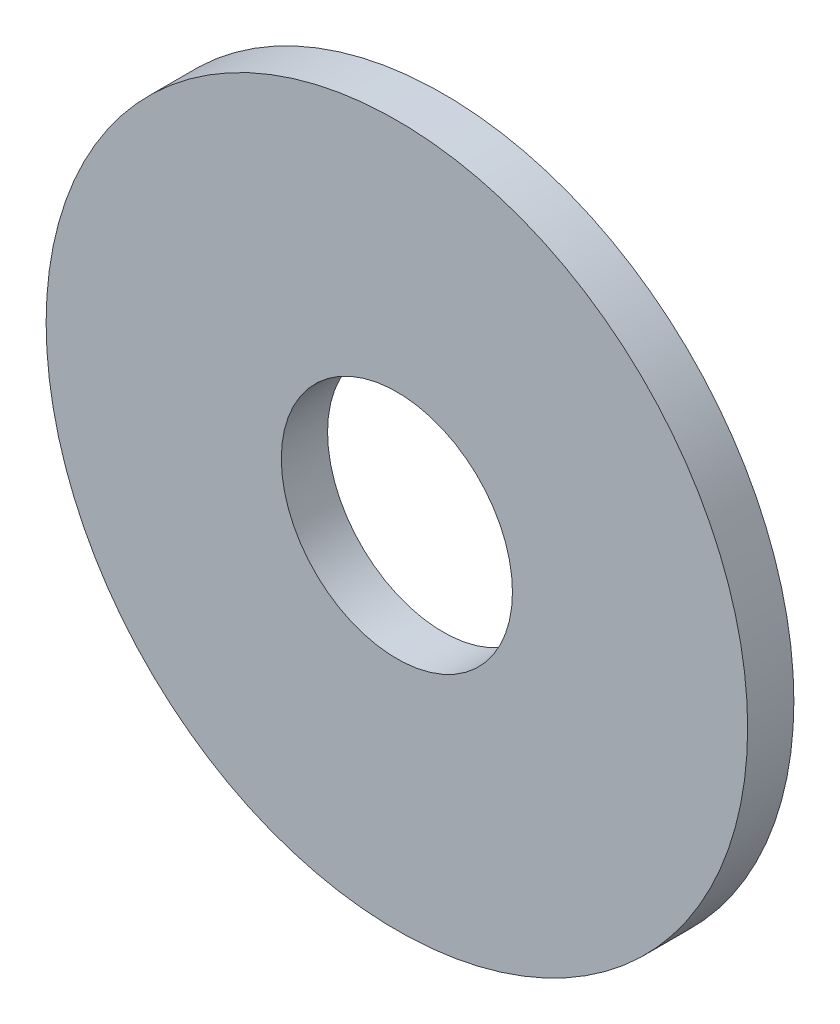
SolidWorks part; units mm, degrees
material "1060 Alloy"
ref_plane "Front Plane" through (0, 0, 0) normal (0, 0, 1) x (1, 0, 0)
ref_plane "Top Plane" through (0, 0, 0) normal (0, 1, 0) x (1, 0, 0)
ref_plane "Right Plane" through (0, 0, 0) normal (1, 0, 0) x (0, 0, -1)
sketch "Sketch1" plane through (0, 0, 0) normal (0, 0, 1) x (1, 0, 0)
  circle A0 centre (0, 0) radius 7.5875
  circle A1 centre (0, 0) radius 2.5
  dimension "D1" = 15.175
  dimension "D2" = 5
extrude "Boss-Extrude1" add sketch "Sketch1" along normal blind 1
equation "\"tubeOutDiameter\" = 35mm"
equation "\"wheelShaftDiameter\"= 12mm"
equation "\"wheelThickness\"= 135mm"
equation "\"BearingDiameter\"= 20mm"
equation "\"BearingThickness\"= 10mm"
equation "\"D1@Sketch1\"=\"wheelShaftDiameter\"+0.125in"
